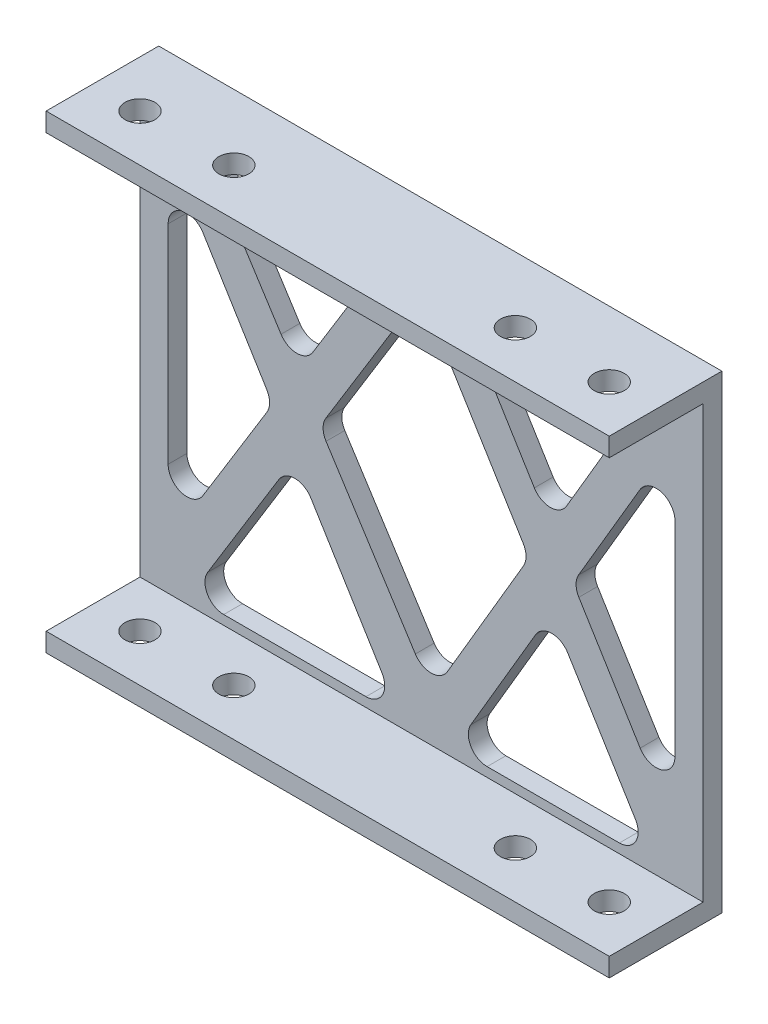
SolidWorks part; units mm, degrees
ref_plane "前视基准面" through (0, 0, 0) normal (0, 0, 1) x (1, 0, 0)
ref_plane "上视基准面" through (0, 0, 0) normal (0, 1, 0) x (1, 0, 0)
ref_plane "右视基准面" through (0, 0, 0) normal (1, 0, 0) x (0, 0, -1)
other "Configuration Table"
sketch "草图1" plane through (0, 0, 0) normal (0, 0, 1) x (1, 0, 0)
  line L0 (-77.9709, -45.8046) -> (-77.9709, -82.1566)
  line L1 (-80.9709, -38.9806) -> (-20.9709, -38.9806)
  line L2 (-80.9709, -38.9806) -> (-80.9709, -88.9806)
  line L3 (-80.9709, -88.9806) -> (-20.9709, -88.9806)
  line L4 (-20.9709, -38.9806) -> (-20.9709, -88.9806)
  line L5 (-75.6243, -85.9806) -> (-53.3174, -85.9806)
  line L6 (-23.9709, -45.9315) -> (-23.9709, -82.1566)
  line L7 (-75.596, -41.9806) -> (-53.3174, -41.9806)
  line L8 (-77.9709, -85.9806) -> (-50.9709, -41.9806) construction
  line L9 (-50.9709, -41.9806) -> (-23.9709, -85.9806) construction
  line L10 (-23.9709, -41.9806) -> (-49.7976, -85.9806) construction
  line L11 (-49.7976, -85.9806) -> (-77.9709, -41.9806) construction
  line L12 (-75.6243, -85.9806) -> (-64.4709, -67.8046)
  line L13 (-50.9709, -45.8046) -> (-39.5035, -64.4921)
  line L14 (-26.29, -41.9806) -> (-37.2091, -60.5832)
  line L15 (-49.8717, -82.1559) -> (-61.8234, -63.4902)
  line L16 (-77.9709, -82.1566) -> (-66.8174, -63.9806)
  line L17 (-25.6957, -40.9682) -> (-49.8717, -82.1559) construction
  line L18 (-23.9709, -45.9315) -> (-34.8385, -64.4463)
  line L19 (-50.9709, -45.8046) -> (-25.6755, -87.0266) construction
  line L20 (-49.7235, -89.8053) -> (-79.6552, -43.0591) construction
  line L21 (-49.8717, -82.1559) -> (-76.2866, -40.9021) construction
  line L22 (-22.2461, -42.993) -> (-49.7235, -89.8053) construction
  line L23 (-79.6755, -84.9346) -> (-50.9709, -38.1566) construction
  line L24 (-48.6243, -41.9806) -> (-37.2091, -60.5832)
  line L25 (-50.9709, -38.1566) -> (-22.2662, -84.9346) construction
  line L26 (-76.2662, -87.0266) -> (-50.9709, -45.8046) construction
  line L27 (-53.3174, -85.9806) -> (-64.4709, -67.8046)
  line L28 (-66.8174, -63.9806) -> (-77.9709, -45.8046)
  line L29 (-64.2198, -59.7475) -> (-53.3174, -41.9806)
  line L30 (-64.2198, -59.7475) -> (-75.596, -41.9806)
  line L31 (-61.8234, -63.4902) -> (-50.9709, -45.8046)
  line L32 (-39.5035, -64.4921) -> (-49.8717, -82.1559)
  line L33 (-37.133, -68.3552) -> (-26.3174, -85.9806)
  line L34 (-37.133, -68.3552) -> (-47.4785, -85.9806)
  line L35 (-34.8385, -64.4463) -> (-23.9709, -82.1566)
  line L36 (-77.9709, -41.9806) -> (-77.9709, -85.9806) construction
  line L37 (-77.9709, -41.9806) -> (-23.9709, -41.9806) construction
  line L38 (-23.9709, -41.9806) -> (-23.9709, -85.9806) construction
  line L39 (-48.6243, -41.9806) -> (-26.29, -41.9806)
  line L40 (-77.9709, -85.9806) -> (-23.9709, -85.9806) construction
  line L41 (-47.4785, -85.9806) -> (-26.3174, -85.9806)
  dimension "D1" = 60
  dimension "D2" = 50
  dimension "D4" = 2
  dimension "D3" = 3
  dimension "D5" = 2
extrude "凸台-拉伸1" add sketch "草图1" along normal blind 2
sketch "草图2" plane through (-20.9709, 0, 0) normal (1, 0, 0) x (0, 0, -1)
  line L0 (-2, -88.9806) -> (-2, -38.9806) construction
  line L1 (-12, -86.9806) -> (-2, -86.9806)
  line L2 (-12, -86.9806) -> (-12, -88.9806)
  line L3 (-12, -88.9806) -> (-2, -88.9806)
  line L4 (-2, -86.9806) -> (-2, -88.9806)
  line L5 (-2, -88.9806) -> (0, -88.9806) construction
  line L6 (0, -63.9806) -> (-23.5667, -63.9806) construction
  line L7 (0, -88.9806) -> (0, -38.9806) construction
  line L8 (-2, -40.9806) -> (-2, -38.9806)
  line L9 (-12, -38.9806) -> (-2, -38.9806)
  line L10 (-12, -40.9806) -> (-12, -38.9806)
  line L11 (-12, -40.9806) -> (-2, -40.9806)
  dimension "D1" = 10
  dimension "D2" = 2
extrude "凸台-拉伸2" add sketch "草图2" against normal blind 60
sketch "草图3" plane through (0, -38.9806, 0) normal (0, 1, 0) x (1, 0, 0)
  line L0 (-75.9709, -7) -> (-65.9709, -7) construction
  line L1 (-80.9709, -12) -> (-80.9709, 0) construction
  line L2 (-80.9709, -12) -> (-20.9709, -12) construction
  line L3 (-50.9709, 0) -> (-50.9709, -12) construction
  line L4 (-20.9709, 0) -> (-80.9709, 0) construction
  circle A0 centre (-75.9709, -7) radius 1.6
  circle A1 centre (-65.9709, -7) radius 1.6
  circle A2 centre (-35.9709, -7) radius 1.6
  circle A3 centre (-25.9709, -7) radius 1.6
  dimension "D1" = 10
  dimension "D4" = 3.2
  dimension "D2" = 5
  dimension "D3" = 5
extrude "切除-拉伸1" cut sketch "草图3" against normal through all
fillet "圆角1" radius 2 22 edges at (-64.4709, -67.8046, 1) (-47.4785, -85.9806, 1) (-37.133, -68.3552, 1) (-66.8174, -63.9806, 1) (-77.9709, -45.8046, 1) (-53.3174, -41.9806, 1) (-39.5035, -64.4921, 1) (-50.9709, -45.8046, 1) (-26.3174, -85.9806, 1) (-53.3174, -85.9806, 1) (-75.6243, -85.9806, 1) (-77.9709, -82.1566, 1) (-64.2198, -59.7475, 1) (-49.8717, -82.1559, 1) (-75.596, -41.9806, 1) (-61.8234, -63.4902, 1) (-48.6243, -41.9806, 1) (-34.8385, -64.4463, 1) (-37.2091, -60.5832, 1) (-26.29, -41.9806, 1) (-23.9709, -45.9315, 1) (-23.9709, -82.1566, 1)
